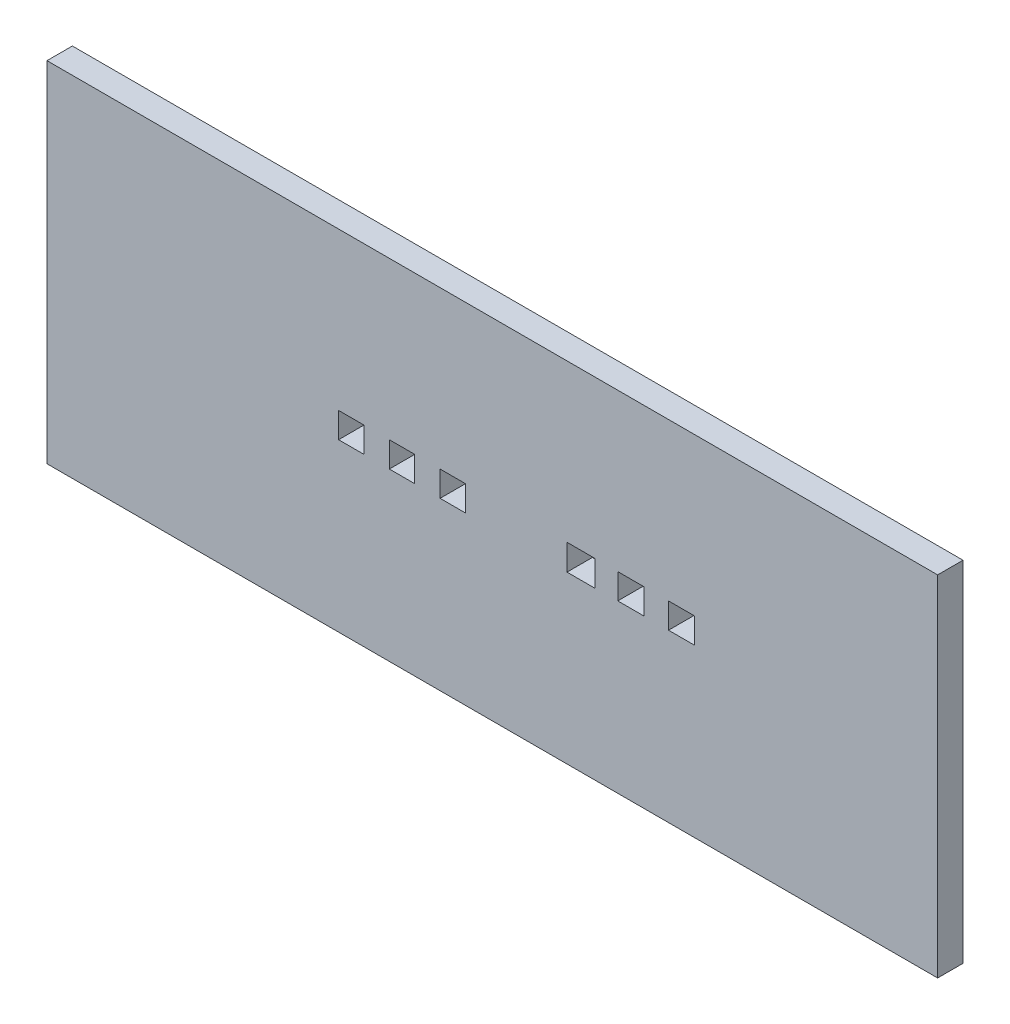
SolidWorks part; units mm, degrees
ref_plane "Front Plane" through (0, 0, 0) normal (0, 0, 1) x (1, 0, 0)
ref_plane "Top Plane" through (0, 0, 0) normal (0, 1, 0) x (1, 0, 0)
ref_plane "Right Plane" through (0, 0, 0) normal (1, 0, 0) x (0, 0, -1)
sketch "Sketch2" plane through (0, 0, 0) normal (0, 0, 1) x (1, 0, 0)
  line L2 (105.4285, -48.0432) -> (-117.4102, -48.0432)
  line L3 (105.4285, -48.0432) -> (105.4285, 39.3073)
  line L4 (105.4285, 39.3073) -> (-117.4102, 39.3073)
  line L5 (-117.4102, -48.0432) -> (-117.4102, 39.3073)
  line L7 (-44.45, 0) -> (-38.1, 0)
  line L8 (-44.45, 0) -> (-44.45, -6.35)
  line L9 (-44.45, -6.35) -> (-38.1, -6.35)
  line L10 (-38.1, 0) -> (-38.1, -6.35)
  line L11 (-31.75, 0) -> (-25.4, 0)
  line L12 (-31.75, 0) -> (-31.75, -6.35)
  line L13 (-31.75, -6.35) -> (-25.4, -6.35)
  line L14 (-25.4, 0) -> (-25.4, -6.35)
  line L15 (-19.05, 0) -> (-12.7, 0)
  line L16 (-19.05, 0) -> (-19.05, -6.35)
  line L17 (-19.05, -6.35) -> (-12.7, -6.35)
  line L18 (-12.7, 0) -> (-12.7, -6.35)
  line L19 (12.7, 0) -> (19.6521, 0)
  line L20 (12.7, 0) -> (12.7, -6.4642)
  line L21 (12.7, -6.4642) -> (19.6521, -6.4642)
  line L22 (19.6521, 0) -> (19.6521, -6.4642)
  line L24 (25.4, 0) -> (31.9555, 0)
  line L25 (25.4, 0) -> (25.4, -6.35)
  line L26 (25.4, -6.35) -> (31.9555, -6.35)
  line L27 (31.9555, 0) -> (31.9555, -6.35)
  line L28 (38.1, 0) -> (44.6555, 0)
  line L29 (38.1, 0) -> (38.1, -6.35)
  line L30 (38.1, -6.35) -> (44.6555, -6.35)
  line L31 (44.6555, 0) -> (44.6555, -6.35)
extrude "Boss-Extrude1" add sketch "Sketch2" along normal blind 6.35
